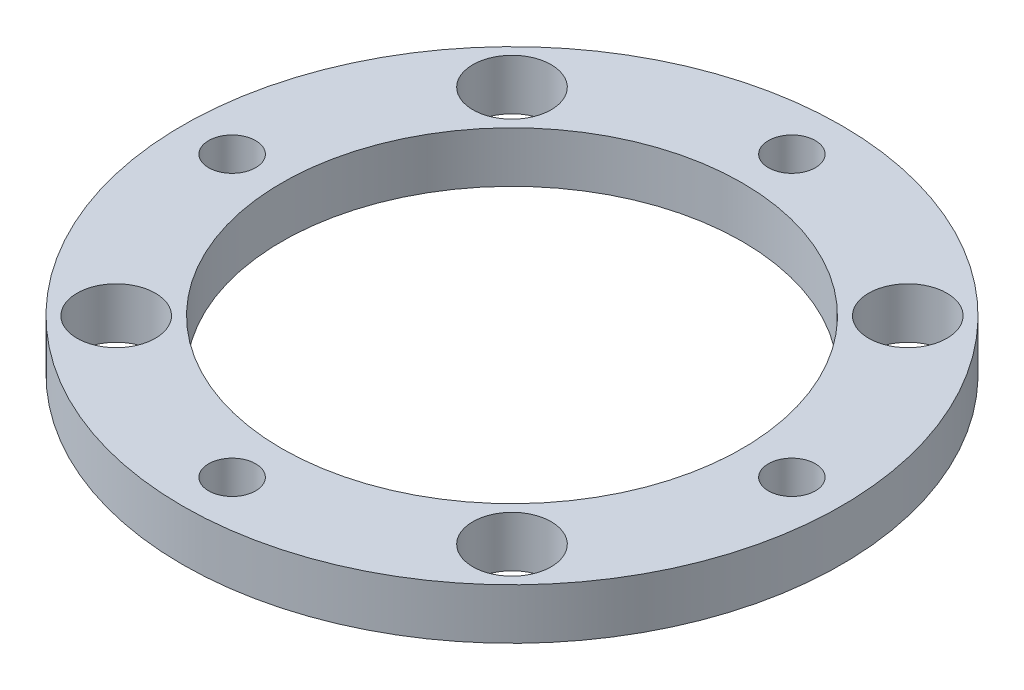
SolidWorks part; units mm, degrees
ref_plane "Top Plane" through (0, 0, 0) normal (0, 0, 1) x (1, 0, 0)
ref_plane "Front Plane" through (0, 0, 0) normal (0, 1, 0) x (1, 0, 0)
ref_plane "Right Plane" through (0, 0, 0) normal (1, 0, 0) x (0, 0, -1)
sketch "Profile Sketch" plane through (0, 0, 0) normal (0, 1, 0) x (1, 0, 0)
  circle A2 centre (0, 0) radius 20.6375
  dimension "D3" = 41.275
extrude "Profile Extrude" add sketch "Profile Sketch" along normal blind 3.175
sketch "Bore Sketch" plane through (0, 0, 0) normal (0, -1, 0) x (-1, 0, 0)
  circle A0 centre (0, 0) radius 14.4145
  dimension "D1" = 28.829
extrude "Bore Cut" cut sketch "Bore Sketch" against normal through all contours A0
sketch "Bolt Clearance Sketch" plane through (0, 0, 0) normal (0, -1, 0) x (1, 0, 0)
  circle A0 centre (0, 17.526) radius 1.4732
  circle A1 centre (17.526, 0) radius 1.4732
  circle A2 centre (0, -17.526) radius 1.4732
  circle A3 centre (-17.526, 0) radius 1.4732
  point P12 (0, 0)
  dimension "D2" = 2.9464
  dimension "D1" = 17.526
  dimension "D3" = 4
extrude "Bolt Clearance Cut" cut sketch "Bolt Clearance Sketch" against normal through all
sketch "Bolt Head Clearance Sketch" plane through (0, 0, 0) normal (0, -1, 0) x (-1, 0, 0)
  line L1 (0, 0) -> (-12.3928, -12.3928) construction
  line L2 (0, 0) -> (-17.526, 0) construction
  line L3 (0, 0) -> (-12.3928, 12.3928) construction
  line L4 (0, 0) -> (0, 17.526) construction
  line L5 (0, 0) -> (12.3928, 12.3928) construction
  line L6 (0, 0) -> (17.526, 0) construction
  line L7 (0, 0) -> (12.3928, -12.3928) construction
  line L8 (0, 0) -> (0, -17.526) construction
  circle A0 centre (-12.3928, -12.3928) radius 2.4511
  circle A3 centre (-12.3928, 12.3928) radius 2.4511
  circle A4 centre (12.3928, 12.3928) radius 2.4511
  circle A5 centre (12.3928, -12.3928) radius 2.4511
  point P19 (0, 0)
  dimension "D1" = 4.9022
  dimension "D2" = 17.526
  dimension "D3" = 45
  dimension "D4" = 4
extrude "Bolt Head Clearance Cut" cut sketch "Bolt Head Clearance Sketch" against normal through all
